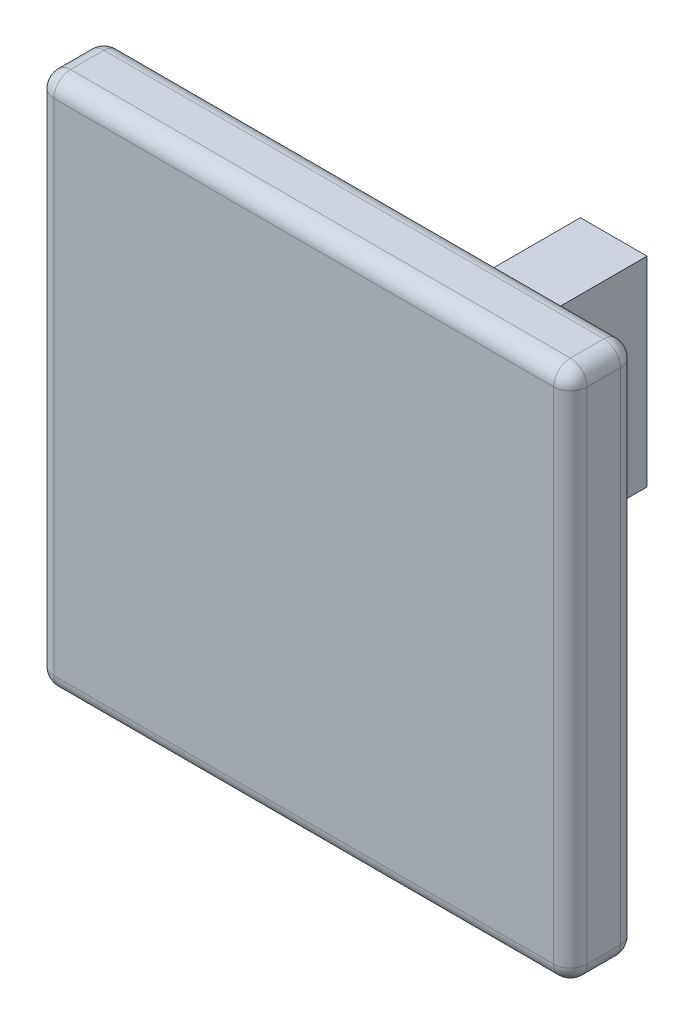
SolidWorks part; units mm, degrees
ref_plane "Front Plane" through (0, 0, 0) normal (0, 0, 1) x (1, 0, 0)
ref_plane "Top Plane" through (0, 0, 0) normal (0, 1, 0) x (1, 0, 0)
ref_plane "Right Plane" through (0, 0, 0) normal (1, 0, 0) x (0, 0, -1)
sketch "Sketch1" plane through (0, 0, 0) normal (0, 1, 0) x (1, 0, 0)
  line L1 (0, 0) -> (2, 0)
  line L2 (0, 0) -> (0, 7.3)
  line L3 (0, 7.3) -> (2, 7.3)
  line L4 (2, 0) -> (2, 7.3)
  dimension "D1" = 7.3
  dimension "D2" = 2
extrude "Boss-Extrude1" add sketch "Sketch1" along normal blind 6
sketch "Sketch3" plane through (0, 0, 0) normal (0, 0, 1) x (1, 0, 0)
  line L1 (-7, 11) -> (9, 11)
  line L2 (-7, 11) -> (-7, -5)
  line L3 (-7, -5) -> (9, -5)
  line L4 (9, 11) -> (9, -5)
  line L6 (0, 6) -> (0, 0) construction
  line L7 (0, 0) -> (2, 0) construction
  dimension "D1" = 16
  dimension "D2" = 16
  dimension "D3" = 7
  dimension "D4" = 11
extrude "Boss-Extrude3" add sketch "Sketch3" along normal blind 2
fillet "Fillet2" radius 0.5 12 edges at (1, 11, 0) (9, 11, 1) (9, 3, 0) (9, -5, 1) (1, -5, 0) (1, 11, 2) (9, 3, 2) (1, -5, 2) (-7, 11, 1) (-7, 3, 2) (-7, -5, 1) (-7, 3, 0)
